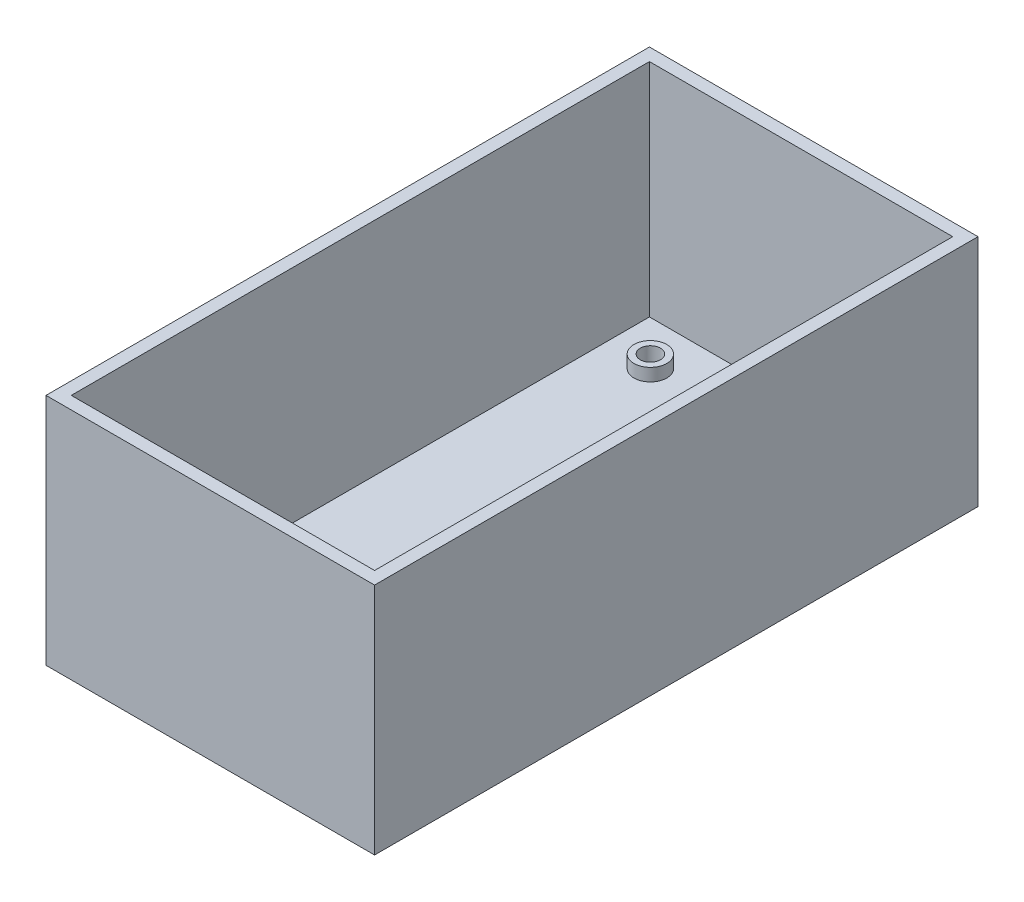
SolidWorks part; units mm, degrees
ref_plane "Front Plane" through (0, 0, 0) normal (0, 0, 1) x (1, 0, 0)
ref_plane "Top Plane" through (0, 0, 0) normal (0, 1, 0) x (1, 0, 0)
ref_plane "Right Plane" through (0, 0, 0) normal (1, 0, 0) x (0, 0, -1)
sketch "Sketch1" plane through (0, 0, 0) normal (0, 1, 0) x (1, 0, 0)
  line L1 (-26, 47.75) -> (26, 47.75)
  line L2 (-26, 47.75) -> (-26, -47.75)
  line L3 (-26, -47.75) -> (26, -47.75)
  line L4 (26, 47.75) -> (26, -47.75)
  line L5 (-26, 47.75) -> (26, -47.75) construction
  line L6 (-26, -47.75) -> (26, 47.75) construction
  point P0 (0, 0)
  dimension "D1" = 52
  dimension "D2" = 95.5
extrude "Boss-Extrude1" add sketch "Sketch1" along normal blind 2
sketch "Sketch2" plane through (0, 2, 0) normal (0, 1, 0) x (1, 0, 0)
  line L0 (0, 47.75) -> (0, -47.75) construction
  line L1 (26, 47.75) -> (-26, 47.75) construction
  line L2 (-26, -47.75) -> (26, -47.75) construction
  line L3 (-26, 0) -> (26, 0) construction
  line L4 (-26, 47.75) -> (-26, -47.75) construction
  line L5 (26, -47.75) -> (26, 47.75) construction
  circle A0 centre (-16.85, 38.75) radius 1.6
  circle A1 centre (16.85, 38.75) radius 1.6
  circle A2 centre (-16.85, -38.75) radius 1.6
  circle A3 centre (16.85, -38.75) radius 1.6
  dimension "D2" = 3.2
  dimension "D3" = 3.2
  dimension "D5" = 3.2
  dimension "D6" = 3.2
  dimension "D1" = 33.7
  dimension "D4" = 16.85
  dimension "D7" = 77.5
  dimension "D8" = 77.5
  dimension "D9" = 38.75
  dimension "D10" = 38.75
extrude "Cut-Extrude1" cut sketch "Sketch2" against normal blind 2
sketch "Sketch3" plane through (0, 2, 0) normal (0, 1, 0) x (1, 0, 0)
  line L0 (24, -45.75) -> (24, 45.75)
  line L1 (24, 45.75) -> (-24, 45.75)
  line L2 (-24, 45.75) -> (-24, -45.75)
  line L3 (-24, -45.75) -> (24, -45.75)
  line L4 (26, -47.75) -> (26, 47.75)
  line L5 (26, 47.75) -> (-26, 47.75)
  line L6 (-26, 47.75) -> (-26, -47.75)
  line L7 (-26, -47.75) -> (26, -47.75)
  line L8 (26, -47.75) -> (26, 47.75)
  line L9 (26, 47.75) -> (-26, 47.75)
  line L10 (-26, 47.75) -> (-26, -47.75)
  line L11 (-26, -47.75) -> (26, -47.75)
  dimension "D1" = 0
  dimension "D2" = 2
extrude "Boss-Extrude2" add sketch "Sketch3" along normal blind 35
sketch "Sketch4" plane through (0, 2, 0) normal (0, 1, 0) x (1, 0, 0)
  line L4 (-24, -45.75) -> (24, -45.75)
  line L5 (24, -45.75) -> (24, 45.75)
  line L6 (24, 45.75) -> (-24, 45.75)
  line L7 (-24, 45.75) -> (-24, -45.75)
  line L8 (-24, -45.75) -> (24, -45.75)
  line L9 (24, -45.75) -> (24, 45.75)
  line L10 (24, 45.75) -> (-24, 45.75)
  line L11 (-24, 45.75) -> (-24, -45.75)
  circle A0 centre (-16.85, 38.75) radius 1.6 construction
  circle A1 centre (-16.85, 38.75) radius 1.6
  circle A2 centre (16.85, 38.75) radius 1.6 construction
  circle A3 centre (16.85, 38.75) radius 1.6
  circle A4 centre (-16.85, -38.75) radius 1.6 construction
  circle A5 centre (-16.85, -38.75) radius 1.6
  circle A6 centre (16.85, -38.75) radius 1.6 construction
  circle A7 centre (16.85, -38.75) radius 1.6
  circle A8 centre (-16.85, -38.75) radius 2.6
  circle A9 centre (16.85, -38.75) radius 2.6
  circle A10 centre (16.85, 38.75) radius 2.6
  circle A11 centre (-16.85, 38.75) radius 2.6
  circle M10 centre (16.85, 38.75) radius 1.6
  circle M11 centre (-16.85, -38.75) radius 1.6
  circle M12 centre (16.85, -38.75) radius 1.6
  circle M13 centre (-16.85, 38.75) radius 1.6
  dimension "D1" = 0
  dimension "D2" = 1
extrude "Boss-Extrude3" add sketch "Sketch4" along normal blind 2 contours A11 M13 | A10 M10 | A9 M12 | A8 M11
